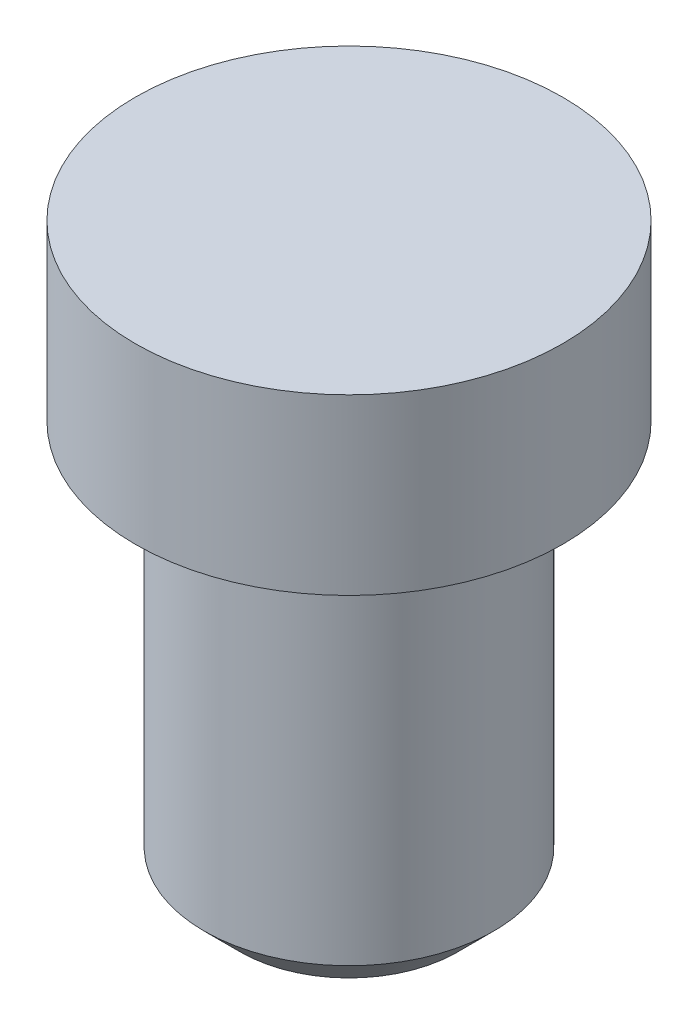
SolidWorks part; units mm, degrees
material "acero"
ref_plane "Alzado" through (0, 0, 0) normal (0, 0, 1) x (1, 0, 0)
ref_plane "Planta" through (0, 0, 0) normal (0, 1, 0) x (1, 0, 0)
ref_plane "Vista lateral" through (0, 0, 0) normal (1, 0, 0) x (0, 0, -1)
sketch "Croquis1" plane through (0, 0, 0) normal (0, 0, 1) x (1, 0, 0)
  line L0 (0, 0) -> (0, -60.9498) construction
  line L1 (0, 0) -> (2.95, 0)
  line L2 (2.95, 0) -> (2.95, -2.4)
  line L3 (2.95, -2.4) -> (2, -2.4)
  line L4 (2, -2.4) -> (2, -8)
  line L5 (2, -8) -> (0, -8)
  line L6 (0, -8) -> (0, 0)
  dimension "D1" = 8
  dimension "D2" = 2.4
  dimension "D3" = 5.9
  dimension "D4" = 4
revolve "Revolución1" add sketch "Croquis1" angle 360 about L0
chamfer "Chaflán1" distance 0.5 angle 45 1 edges at (0, -8, 2)
